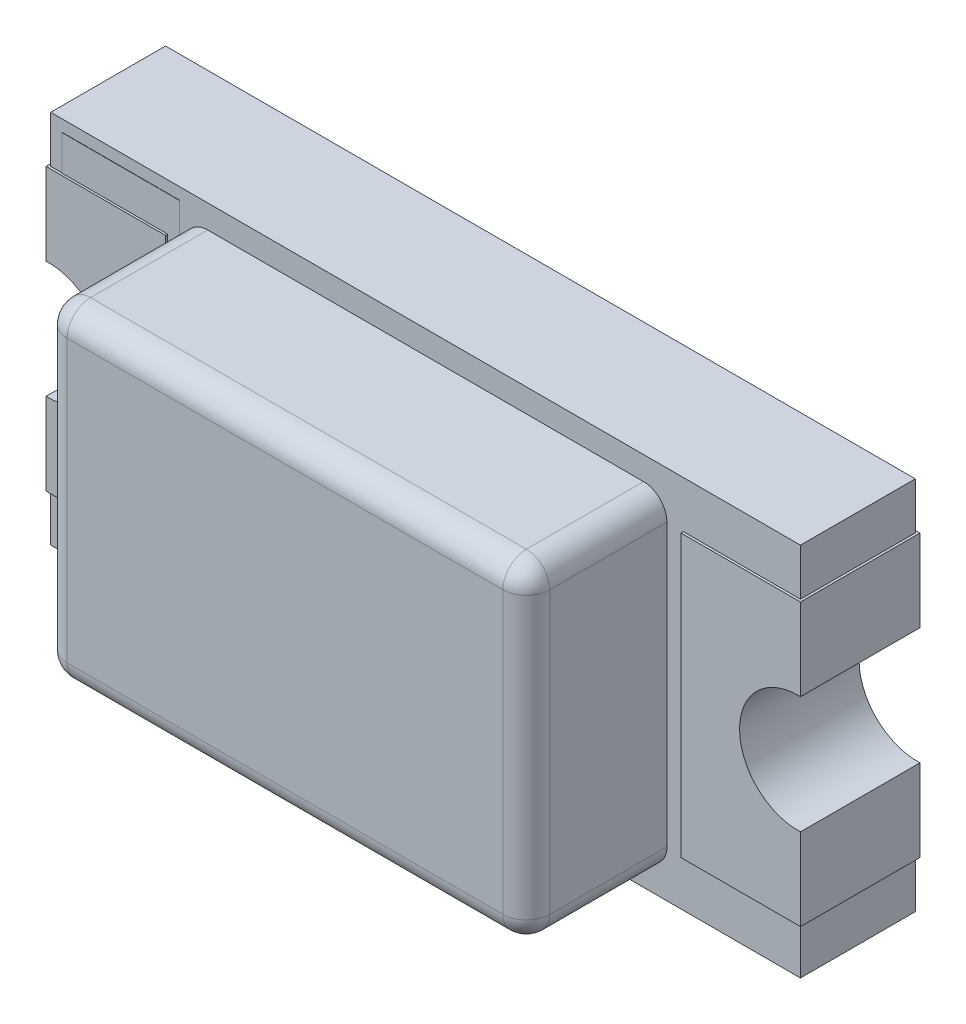
SolidWorks part; units mm, degrees
ref_plane "Спереди" through (0, 0, 0) normal (0, 0, 1) x (1, 0, 0)
ref_plane "Сверху" through (0, 0, 0) normal (0, 1, 0) x (1, 0, 0)
ref_plane "Справа" through (0, 0, 0) normal (1, 0, 0) x (0, 0, -1)
sketch "Эскиз2" plane through (0, 0, 0) normal (0, 0, 1) x (1, 0, 0)
  line L1 (-1.6, 0.8) -> (1.6, 0.8)
  line L2 (-1.6, 0.8) -> (-1.6, -0.8)
  line L3 (-1.6, -0.8) -> (1.6, -0.8)
  line L4 (1.6, 0.8) -> (1.6, -0.8)
  point P0 (0, 0)
extrude "Бобышка-Вытянуть1" add sketch "Эскиз2" along normal blind 0.49 from offset 0.01
sketch "Эскиз3" plane through (0, 0, 0) normal (0, 0, 1) x (1, 0, 0)
  line L1 (-1.61, 0.6) -> (-1.1, 0.6)
  line L2 (-1.61, 0.6) -> (-1.61, -0.6)
  line L3 (-1.61, -0.6) -> (-1.1, -0.6)
  line L4 (-1.1, 0.6) -> (-1.1, -0.6)
  line L5 (1.1, 0.6) -> (1.61, 0.6)
  line L6 (1.1, 0.6) -> (1.1, -0.6)
  line L7 (1.1, -0.6) -> (1.61, -0.6)
  line L8 (1.61, 0.6) -> (1.61, -0.6)
extrude "Бобышка-Вытянуть2" add sketch "Эскиз3" along normal blind 0.51
sketch "Эскиз4" plane through (0, 0, 0) normal (0, 0, 1) x (1, 0, 0)
  line L1 (-1.03, 0.7) -> (1.03, 0.7)
  line L2 (-1.03, 0.7) -> (-1.03, -0.7)
  line L3 (-1.03, -0.7) -> (1.03, -0.7)
  line L4 (1.03, 0.7) -> (1.03, -0.7)
extrude "Бобышка-Вытянуть3" add sketch "Эскиз4" along normal blind 0.6 from offset 0.5
fillet "Скругление1" radius 0.1 8 edges at (1.03, 0.7, 0.8) (-1.03, 0.7, 0.8) (0, 0.7, 1.1) (1.03, 0, 1.1) (1.03, -0.7, 0.8) (-1.03, -0.7, 0.8) (0, -0.7, 1.1) (-1.03, 0, 1.1)
sketch "Эскиз5" plane through (0, 0, 0.5) normal (0, 0, 1) x (1, 0, 0)
  line L5 (-1.55, 0.75) -> (-1.05, 0.75)
  line L6 (-1.55, 0.75) -> (-1.55, -0.75)
  line L7 (-1.55, -0.75) -> (-1.05, -0.75)
  line L8 (-1.05, 0.75) -> (-1.05, -0.75)
extrude "Бобышка-Вытянуть4" add sketch "Эскиз5" along normal blind 0.001
sketch "Эскиз6" plane through (0, 0, 0) normal (0, 0, 1) x (1, 0, 0)
  circle A0 centre (-1.6, 0) radius 0.25
  circle A1 centre (1.6, 0) radius 0.25
extrude "Вырез-Вытянуть2" cut sketch "Эскиз6" along normal blind 0.52
